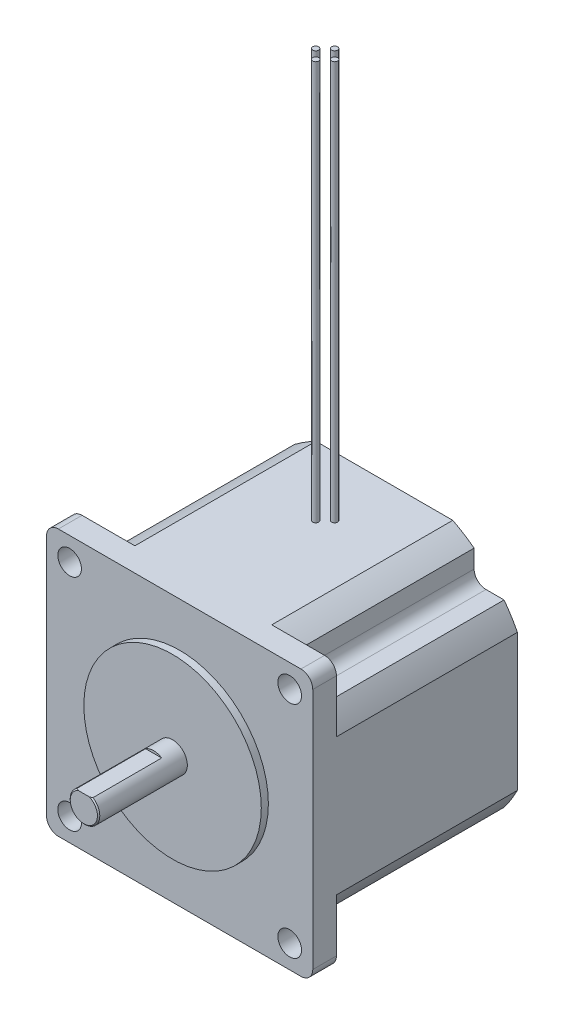
SolidWorks part; units mm, degrees
material "Plain Carbon Steel"
ref_plane "Front Plane" through (0, 0, 0) normal (0, 0, 1) x (1, 0, 0)
ref_plane "Top Plane" through (0, 0, 0) normal (0, 1, 0) x (1, 0, 0)
ref_plane "Right Plane" through (0, 0, 0) normal (1, 0, 0) x (0, 0, -1)
ref_plane "Plane1" through (0, 0, 43.942) normal (0, 0, 1) x (1, 0, 0)
sketch "Sketch1" plane through (0, 0, 43.942) normal (0, 0, 1) x (1, 0, 0)
  line L0 (28.575, -28.575) -> (28.575, 28.575)
  line L1 (28.575, 28.575) -> (-28.575, 28.575)
  line L2 (-28.575, 28.575) -> (-28.575, -28.575)
  line L3 (-28.575, -28.575) -> (28.575, -28.575)
extrude "Boss-Extrude1" add sketch "Sketch1" against normal blind 43.942
sketch "Sketch2" plane through (0, 0, 0) normal (0, 0, -1) x (-1, 0, 0)
  line L0 (-28.575, -28.575) -> (-14.6925, -28.575)
  line L1 (-28.575, -14.6925) -> (-28.575, -28.575)
  arc A0 (-14.6925, -28.575) -> (-28.575, -14.6925) centre (0, 0) cw
extrude "Cut-Extrude1" cut sketch "Sketch2" against normal blind 38.862
sketch "Sketch3" plane through (0, 0, 0) normal (0, 0, -1) x (-1, 0, 0)
  line L0 (-19.2786, -25.7048) -> (-19.2786, -19.2786)
  line L1 (-19.2786, -19.2786) -> (-25.7048, -19.2786)
  arc A0 (-25.7048, -19.2786) -> (-19.2786, -25.7048) centre (0, 0) ccw
extrude "Cut-Extrude2" cut sketch "Sketch3" against normal blind 38.862
sketch "Sketch4" plane through (0, 0, 0) normal (0, 0, -1) x (-1, 0, 0)
  line L0 (-28.575, 28.575) -> (-28.575, 14.6925)
  line L1 (-14.6925, 28.575) -> (-28.575, 28.575)
  arc A0 (-28.575, 14.6925) -> (-14.6925, 28.575) centre (0, 0) cw
extrude "Cut-Extrude3" cut sketch "Sketch4" against normal blind 38.862
sketch "Sketch5" plane through (0, 0, 0) normal (0, 0, -1) x (-1, 0, 0)
  line L0 (-25.7048, 19.2786) -> (-19.2786, 19.2786)
  line L1 (-19.2786, 19.2786) -> (-19.2786, 25.7048)
  arc A0 (-19.2786, 25.7048) -> (-25.7048, 19.2786) centre (0, 0) ccw
extrude "Cut-Extrude4" cut sketch "Sketch5" against normal blind 38.862
sketch "Sketch6" plane through (0, 0, 0) normal (0, 0, -1) x (-1, 0, 0)
  line L0 (28.575, 28.575) -> (14.6925, 28.575)
  line L1 (28.575, 14.6925) -> (28.575, 28.575)
  arc A0 (14.6925, 28.575) -> (28.575, 14.6925) centre (0, 0) cw
extrude "Cut-Extrude5" cut sketch "Sketch6" against normal blind 38.862
sketch "Sketch7" plane through (0, 0, 0) normal (0, 0, -1) x (-1, 0, 0)
  line L0 (19.2786, 25.7048) -> (19.2786, 19.2786)
  line L1 (19.2786, 19.2786) -> (25.7048, 19.2786)
  arc A0 (25.7048, 19.2786) -> (19.2786, 25.7048) centre (0, 0) ccw
extrude "Cut-Extrude6" cut sketch "Sketch7" against normal blind 38.862
sketch "Sketch8" plane through (0, 0, 0) normal (0, 0, -1) x (-1, 0, 0)
  line L0 (28.575, -28.575) -> (28.575, -14.6925)
  line L1 (14.6925, -28.575) -> (28.575, -28.575)
  arc A0 (28.575, -14.6925) -> (14.6925, -28.575) centre (0, 0) cw
extrude "Cut-Extrude7" cut sketch "Sketch8" against normal blind 38.862
sketch "Sketch9" plane through (0, 0, 0) normal (0, 0, -1) x (-1, 0, 0)
  line L0 (25.7048, -19.2786) -> (19.2786, -19.2786)
  line L1 (19.2786, -19.2786) -> (19.2786, -25.7048)
  arc A0 (19.2786, -25.7048) -> (25.7048, -19.2786) centre (0, 0) ccw
extrude "Cut-Extrude8" cut sketch "Sketch9" against normal blind 38.862
sketch "Sketch10" plane through (0, 0, 43.942) normal (0, 0, 1) x (1, 0, 0)
  circle A0 centre (0, 0) radius 19.05
extrude "Boss-Extrude2" add sketch "Sketch10" along normal blind 1.524
sketch "Sketch11" plane through (0, 0, 45.466) normal (0, 0, 1) x (1, 0, 0)
  circle A0 centre (0, 0) radius 3.175
extrude "Boss-Extrude3" add sketch "Sketch11" along normal blind 19.05
sketch "Sketch12" plane through (0, 0, 64.516) normal (0, 0, 1) x (1, 0, 0)
  line L0 (-1.7227, 2.667) -> (1.7227, 2.667)
  arc A0 (1.7227, 2.667) -> (-1.7227, 2.667) centre (0, 0) ccw
extrude "Cut-Extrude9" cut sketch "Sketch12" against normal blind 14.986
ref_plane "Plane2" through (0, 0, 12.7) normal (0, 0, -1) x (-1, 0, 0)
sketch "Sketch13" plane through (0, 0, 12.7) normal (0, 0, -1) x (-1, 0, 0)
  line L0 (1.397, 28.575) -> (2.032, 28.575)
  line L1 (2.032, 28.575) -> (2.032, 114.3)
  line L2 (2.032, 114.3) -> (1.397, 114.3)
  line L3 (1.397, 114.3) -> (1.397, 28.575)
  line L4 (2.032, 28.575) -> (2.032, 114.3) construction
revolve "Revolve1" add sketch "Sketch13" angle 360 about L4
sketch "Sketch14" plane through (0, 0, 12.7) normal (0, 0, -1) x (-1, 0, 0)
  line L0 (-2.667, 28.575) -> (-2.032, 28.575)
  line L1 (-2.032, 28.575) -> (-2.032, 114.3)
  line L2 (-2.032, 114.3) -> (-2.667, 114.3)
  line L3 (-2.667, 114.3) -> (-2.667, 28.575)
  line L4 (-2.032, 28.575) -> (-2.032, 114.3) construction
revolve "Revolve2" add sketch "Sketch14" angle 360 about L4
ref_plane "Plane3" through (0, 0, 14.732) normal (0, 0, -1) x (-1, 0, 0)
sketch "Sketch15" plane through (0, 0, 14.732) normal (0, 0, -1) x (-1, 0, 0)
  line L0 (-0.635, 28.575) -> (0, 28.575)
  line L1 (0, 28.575) -> (0, 114.3)
  line L2 (0, 114.3) -> (-0.635, 114.3)
  line L3 (-0.635, 114.3) -> (-0.635, 28.575)
  line L4 (0, 28.575) -> (0, 114.3) construction
revolve "Revolve3" add sketch "Sketch15" angle 360 about L4
ref_plane "Plane4" through (0, 0, 10.668) normal (0, 0, -1) x (-1, 0, 0)
sketch "Sketch16" plane through (0, 0, 10.668) normal (0, 0, -1) x (-1, 0, 0)
  line L0 (-0.635, 28.575) -> (0, 28.575)
  line L1 (0, 28.575) -> (0, 114.3)
  line L2 (0, 114.3) -> (-0.635, 114.3)
  line L3 (-0.635, 114.3) -> (-0.635, 28.575)
  line L4 (0, 28.575) -> (0, 114.3) construction
revolve "Revolve4" add sketch "Sketch16" angle 360 about L4
hole_wizard "Hole1" positions "Sketch18" profile "Sketch17" legacy
sketch "Sketch18" plane through (0, 0, 38.862) normal (0, 0, -1) x (-1, 0, 0)
  point P0 (23.622, -23.622)
sketch "Sketch17" plane through (-23.622, -23.622, 38.862) normal (1, 0, 0) x (0, 1, 0)
  line L0 (0, 0) -> (0, 25.654)
  line L1 (0, 25.654) -> (2.54, 25.654)
  line L2 (2.54, 25.654) -> (2.54, 0)
  line L3 (2.54, 0) -> (0, 0)
  line L4 (0, 110) -> (0, -10) construction
  dimension "Diameter" = 5.08
  dimension "Depth" = 25.654
hole_wizard "Hole2" positions "Sketch20" profile "Sketch19" legacy
sketch "Sketch20" plane through (0, 0, 38.862) normal (0, 0, -1) x (-1, 0, 0)
  point P0 (23.622, 23.622)
sketch "Sketch19" plane through (-23.622, 23.622, 38.862) normal (1, 0, 0) x (0, 1, 0)
  line L0 (0, 0) -> (0, 25.654)
  line L1 (0, 25.654) -> (2.54, 25.654)
  line L2 (2.54, 25.654) -> (2.54, 0)
  line L3 (2.54, 0) -> (0, 0)
  line L4 (0, 110) -> (0, -10) construction
  dimension "Diameter" = 5.08
  dimension "Depth" = 25.654
hole_wizard "Hole3" positions "Sketch22" profile "Sketch21" legacy
sketch "Sketch22" plane through (0, 0, 38.862) normal (0, 0, -1) x (-1, 0, 0)
  point P0 (-23.622, 23.622)
sketch "Sketch21" plane through (23.622, 23.622, 38.862) normal (1, 0, 0) x (0, 1, 0)
  line L0 (0, 0) -> (0, 25.654)
  line L1 (0, 25.654) -> (2.54, 25.654)
  line L2 (2.54, 25.654) -> (2.54, 0)
  line L3 (2.54, 0) -> (0, 0)
  line L4 (0, 110) -> (0, -10) construction
  dimension "Diameter" = 5.08
  dimension "Depth" = 25.654
hole_wizard "Hole4" positions "Sketch24" profile "Sketch23" legacy
sketch "Sketch24" plane through (0, 0, 38.862) normal (0, 0, -1) x (-1, 0, 0)
  point P0 (-23.622, -23.622)
sketch "Sketch23" plane through (23.622, -23.622, 38.862) normal (1, 0, 0) x (0, 1, 0)
  line L0 (0, 0) -> (0, 25.654)
  line L1 (0, 25.654) -> (2.54, 25.654)
  line L2 (2.54, 25.654) -> (2.54, 0)
  line L3 (2.54, 0) -> (0, 0)
  line L4 (0, 110) -> (0, -10) construction
  dimension "Diameter" = 5.08
  dimension "Depth" = 25.654
chamfer "Chamfer1" distance 0.254 angle 45 1 edges at (0, -3.175, 64.516)
fillet "Fillet1" radius 2.54 1 edges at (-28.575, 28.575, 41.402)
fillet "Fillet2" radius 2.54 1 edges at (-28.575, -28.575, 41.402)
fillet "Fillet3" radius 2.54 1 edges at (28.575, 28.575, 41.402)
fillet "Fillet4" radius 2.54 1 edges at (-19.2786, 19.2786, 19.431)
fillet "Fillet5" radius 2.54 1 edges at (28.575, -28.575, 41.402)
fillet "Fillet6" radius 2.54 1 edges at (19.2786, -19.2786, 19.431)
fillet "Fillet7" radius 2.54 1 edges at (19.2786, 19.2786, 19.431)
fillet "Fillet8" radius 2.54 1 edges at (-19.2786, -19.2786, 19.431)
